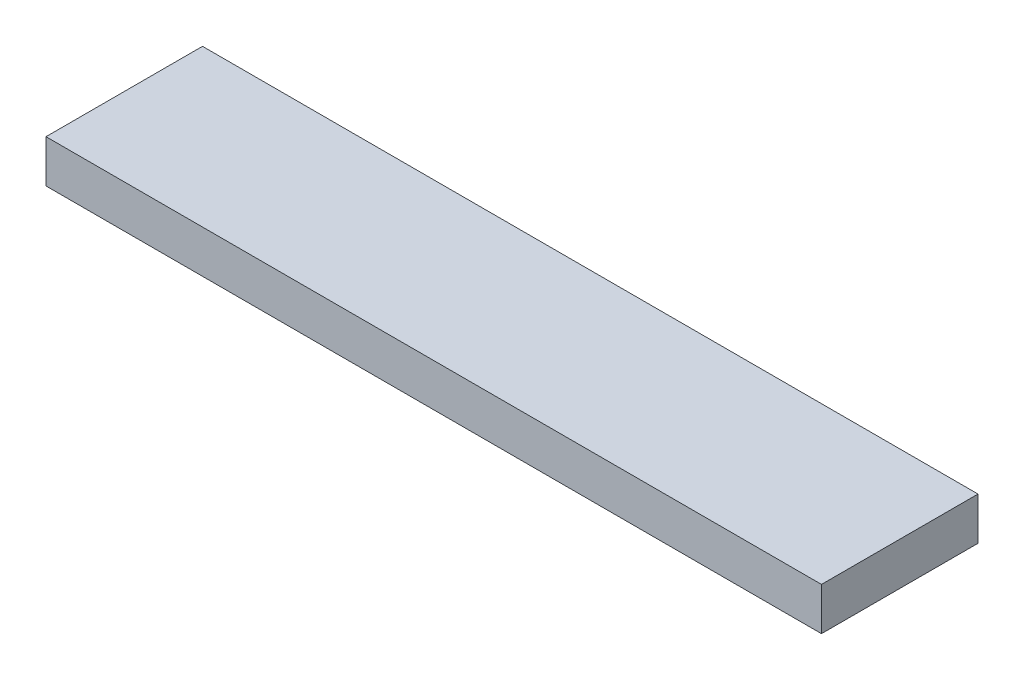
SolidWorks part; units mm, degrees
ref_plane "Front Plane" through (0, 0, 0) normal (0, 0, 1) x (1, 0, 0)
ref_plane "Top Plane" through (0, 0, 0) normal (0, 1, 0) x (1, 0, 0)
ref_plane "Right Plane" through (0, 0, 0) normal (1, 0, 0) x (0, 0, -1)
sketch "Sketch1" plane through (0, 0, 0) normal (0, 1, 0) x (1, 0, 0)
  line L1 (0, 0) -> (692.15, 0)
  line L2 (0, 0) -> (0, 139.7)
  line L3 (0, 139.7) -> (692.15, 139.7)
  line L4 (692.15, 0) -> (692.15, 139.7)
  dimension "D1" = 139.7
  dimension "D2" = 692.15
extrude "Boss-Extrude1" add sketch "Sketch1" along normal blind 38.1
